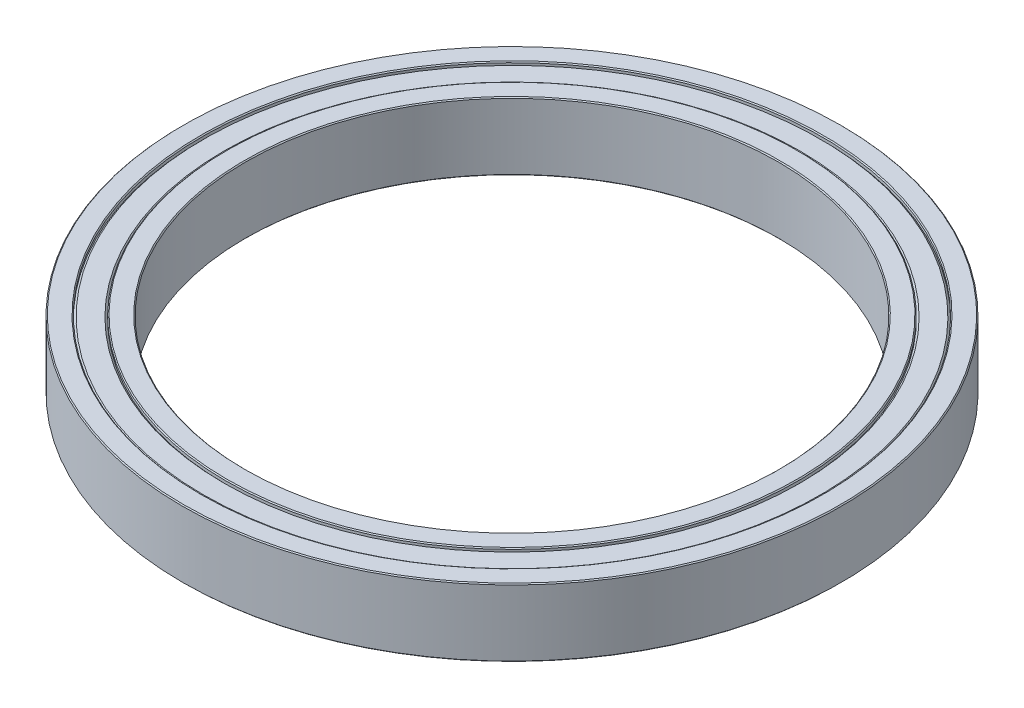
SolidWorks part; units mm, degrees
ref_plane "Front Plane" through (0, 0, 0) normal (0, 0, 1) x (1, 0, 0)
ref_plane "Top Plane" through (0, 0, 0) normal (0, 1, 0) x (1, 0, 0)
ref_plane "Right Plane" through (0, 0, 0) normal (1, 0, 0) x (0, 0, -1)
sketch "Sketch1" plane through (0, 0, 0) normal (1, 0, 0) x (0, 0, -1)
  line L1 (0, 3.5) -> (34, 3.5)
  line L2 (0, 3.5) -> (0, -3.5) construction
  line L3 (0, -3.5) -> (34, -3.5)
  line L4 (34, 3.5) -> (34, -3.5)
  line L6 (32.6, 0) -> (0, 0) construction
  line L7 (27.5, 3.5) -> (27.5, -3.5)
  dimension "D1" = 7
  dimension "D2" = 34
  dimension "D3" = 1.4
  dimension "D5" = 55
revolve "Revolve1" add sketch "Sketch1" angle 360 about L2
sketch "Sketch3" plane through (0, 0, 0) normal (1, 0, 0) x (0, 0, -1)
  line L0 (34, 3.5) -> (34, -3.5) construction
  line L1 (27.5, 3.5) -> (27.5, -3.5) construction
  line L2 (0, 3.5) -> (34, 3.5) construction
  line L3 (34, 3.5) -> (34, -3.5) construction
  line L4 (27.5, 3.5) -> (27.5, -3.5)
  line L5 (0, 3.5) -> (34, 3.5) construction
  line L6 (29.5, 3.5) -> (32, 3.5)
  line L7 (29.5, 3.5) -> (29.5, 3.1)
  line L8 (29.5, 3.1) -> (29.7, 3.3)
  line L9 (29.7, 3.3) -> (31.8, 3.3)
  line L10 (31.8, 3.3) -> (32, 3.1)
  line L11 (32, 3.1) -> (32, 3.5)
  line L14 (0, 3.5) -> (0, -3.5) construction
  line L17 (0, 3.5) -> (0, -3.5) construction
  line L18 (29.5, 3.1) -> (32, 3.1) construction
  line L19 (30.75, 3.1) -> (30.75, 3.5) construction
  dimension "D1" = 2
  dimension "D2" = 0.2
  dimension "D3" = 2
  dimension "D4" = 0.2
  dimension "D5" = 0.2
revolve "Cut-Revolve2" cut sketch "Sketch3" angle 360 about L17
mirror "Mirror1" about plane through (0, 0, 0) normal (0, 1, 0) of "Cut-Revolve2"
chamfer "Chamfer1" distance 0.1 angle 45 8 edges at (0, -3.5, 32) (0, 3.5, 32) (0, -3.5, 34) (0, 3.5, 34) (0, -3.5, 29.5) (0, 3.5, 29.5) (0, -3.5, 27.5) (0, 3.5, 27.5)
